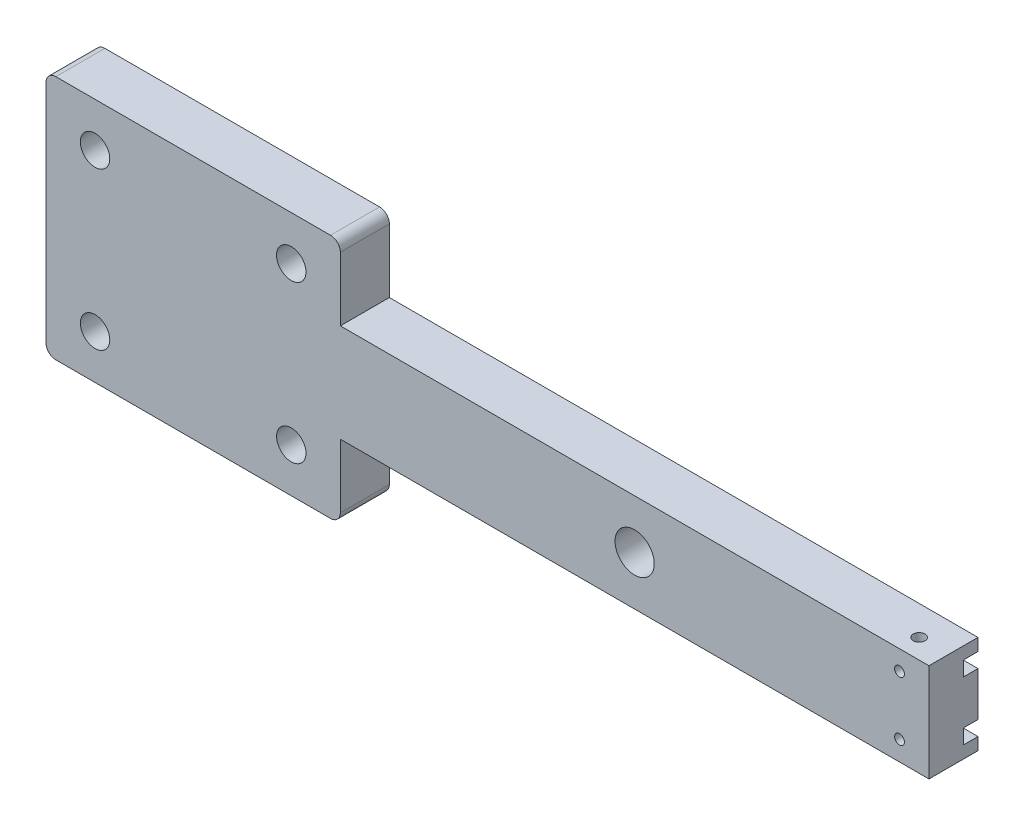
SolidWorks part; units mm, degrees
material "PTFE (general)"
ref_plane "Front Plane" through (0, 0, 0) normal (0, 0, 1) x (1, 0, 0)
ref_plane "Top Plane" through (0, 0, 0) normal (0, 1, 0) x (1, 0, 0)
ref_plane "Right Plane" through (0, 0, 0) normal (1, 0, 0) x (0, 0, -1)
sketch "Sketch1" plane through (0, 0, 0) normal (0, 0, 1) x (1, 0, 0)
  line L0 (0, 25) -> (180, 25) construction
  line L1 (0, 0) -> (60, 0)
  line L2 (0, 0) -> (0, 50)
  line L3 (0, 50) -> (60, 50)
  line L4 (60, 0) -> (60, 15)
  line L5 (60, 15) -> (180, 15)
  line L7 (60, 35) -> (180, 35)
  line L8 (180, 15) -> (180, 35)
  line L10 (60, 35) -> (60, 50)
  dimension "D1" = 60
  dimension "D2" = 120
  dimension "D3" = 20
  dimension "D4" = 50
extrude "Boss-Extrude1" add sketch "Sketch1" along normal blind 10
sketch "Sketch2" plane through (0, 0, 10) normal (0, 0, 1) x (1, 0, 0)
  line L0 (0, 25) -> (180, 25) construction
  line L1 (0, 50) -> (0, 0) construction
  line L2 (180, 15) -> (180, 35) construction
  line L3 (30, 0) -> (30, 50) construction
  line L4 (0, 0) -> (60, 0) construction
  line L5 (60, 50) -> (0, 50) construction
  circle A0 centre (10, 9) radius 3
  circle A1 centre (50, 9) radius 3
  circle A2 centre (50, 41) radius 3
  circle A3 centre (10, 41) radius 3
  dimension "D1" = 6
  dimension "D2" = 20
  dimension "D3" = 16
extrude "Cut-Extrude1" cut sketch "Sketch2" against normal offset from surface (7 mm away) 3 up to face at (75, 25, 0)
sketch "Sketch4" plane through (0, 0, 0) normal (0, 0, -1) x (-1, 0, 0)
  line L0 (-50, 25) -> (-10, 25) construction
  line L1 (-50, 5) -> (-10, 5)
  line L2 (-50, 5) -> (-50, 45)
  line L3 (-50, 45) -> (-10, 45)
  line L4 (-10, 5) -> (-10, 45)
  line L5 (-30, 5) -> (-30, 45) construction
  line L6 (0, 25) -> (-180, 25) construction
  line L7 (0, 50) -> (0, 0) construction
  line L8 (-180, 15) -> (-180, 35) construction
  line L9 (-30, 0) -> (-30, 25) construction
  line L10 (0, 0) -> (-60, 0) construction
  dimension "D1" = 40
  dimension "D2" = 40
extrude "Cut-Extrude3" cut sketch "Sketch4" against normal blind 3
sketch "Sketch5" plane through (0, 0, 0) normal (0, 0, -1) x (-1, 0, 0)
  line L0 (-180, 25) -> (0, 25) construction
  line L1 (-180, 15) -> (-180, 35) construction
  line L2 (0, 50) -> (0, 0) construction
  circle A0 centre (-174, 31) radius 1
  circle A1 centre (-174, 19) radius 1
  circle A2 centre (-120, 25) radius 4
  dimension "D1" = 2
  dimension "D4" = 8
  dimension "D5" = 120
  dimension "D2" = 6
  dimension "D3" = 6
extrude "Cut-Extrude4" cut sketch "Sketch5" against normal through all
sketch "Sketch6" plane through (180, 0, 0) normal (1, 0, 0) x (0, 0, -1)
  line L0 (0, 25) -> (-10, 25) construction
  line L1 (0, 15) -> (0, 35) construction
  line L2 (-10, 15) -> (-10, 35) construction
  line L4 (-3, 31) -> (0, 31) construction
  line L5 (0, 32.5) -> (-3, 32.5)
  line L6 (0, 32.5) -> (0, 29.5)
  line L7 (0, 29.5) -> (-3, 29.5)
  line L8 (-3, 32.5) -> (-3, 29.5)
  line L9 (0, 17.5) -> (0, 20.5)
  line L10 (0, 17.5) -> (-3, 17.5)
  line L11 (-3, 17.5) -> (-3, 20.5)
  line L12 (0, 20.5) -> (-3, 20.5)
  dimension "D2" = 6
  dimension "D1" = 3
  dimension "D3" = 3
extrude "Cut-Extrude5" cut sketch "Sketch6" against normal up to surface (130 mm away) up to face at (50, 25, 2.25)
fillet "Fillet1" radius 2 4 edges at (0, 0, 5) (60, 0, 5) (0, 50, 5) (60, 50, 5)
sketch "Sketch7" plane through (0, 35, 0) normal (0, 1, 0) x (1, 0, 0)
  line L0 (180, -10) -> (180, 0) construction
  line L1 (180, -10) -> (60, -10) construction
  circle A0 centre (174, -6) radius 1.2
  dimension "D3" = 2.4
  dimension "D1" = 6
  dimension "D2" = 4
extrude "Cut-Extrude6" cut sketch "Sketch7" against normal through all
